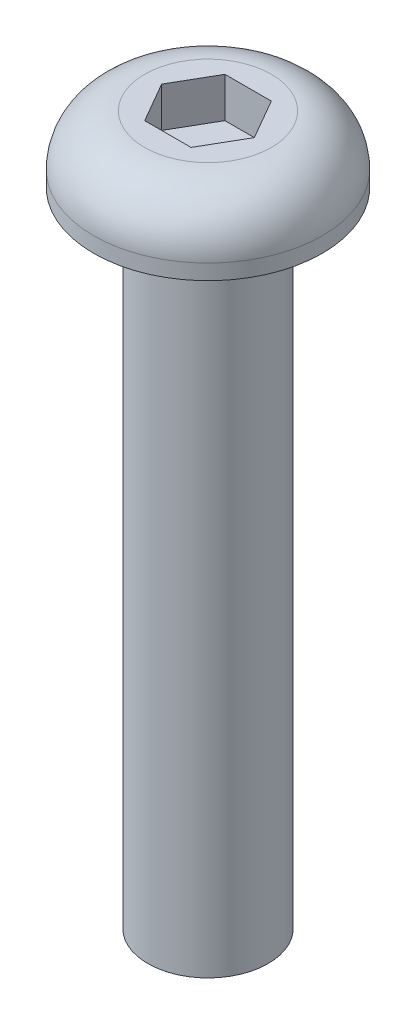
SolidWorks part; units mm, degrees
material "AISI 304"
ref_plane "Front Plane" through (0, 0, 0) normal (0, 0, 1) x (1, 0, 0)
ref_plane "Top Plane" through (0, 0, 0) normal (0, 1, 0) x (1, 0, 0)
ref_plane "Right Plane" through (0, 0, 0) normal (1, 0, 0) x (0, 0, -1)
sketch "Sketch1" plane through (0, 0, 0) normal (0, 0, 1) x (1, 0, 0)
  line L0 (1.5, 0) -> (2.85, 0)
  line L1 (2.85, 0) -> (2.85, 0.38)
  line L2 (1.58, 1.65) -> (0, 1.65)
  line L3 (1.5, 0) -> (1.5, -16)
  line L4 (1.5, -16) -> (0, -16)
  line L5 (0, -16) -> (0, 1.65)
  arc A0 (2.85, 0.38) -> (1.58, 1.65) centre (1.58, 0.38) ccw
  dimension "D1" = 1.5
  dimension "D2" = 16
  dimension "D3" = 2.85
  dimension "D4" = 1.65
  dimension "D5" = 0.38
revolve "Revolve1" add sketch "Sketch1" angle 360 about L5
sketch "Sketch2" plane through (0, 1.65, 0) normal (0, 1, 0) x (1, 0, 0)
  line L1 (0.5774, 1) -> (-0.5774, 1)
  line L2 (-0.5774, 1) -> (-1.1547, 0)
  line L3 (-1.1547, 0) -> (-0.5774, -1)
  line L4 (-0.5774, -1) -> (0.5774, -1)
  line L5 (0.5774, -1) -> (1.1547, 0)
  line L6 (1.1547, 0) -> (0.5774, 1)
  circle A0 centre (0, 0) radius 1 construction
  dimension "D1" = 2
extrude "Cut-Extrude1" cut sketch "Sketch2" against normal blind 1
